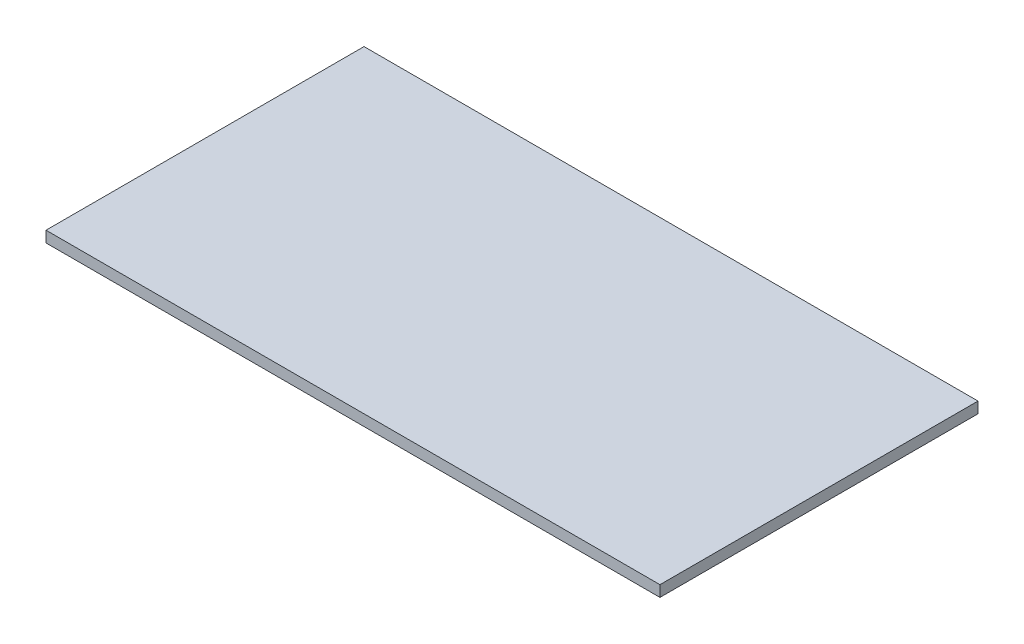
SolidWorks part; units mm, degrees
ref_plane "前视基准面" through (0, 0, 0) normal (0, 0, 1) x (1, 0, 0)
ref_plane "上视基准面" through (0, 0, 0) normal (0, 1, 0) x (1, 0, 0)
ref_plane "右视基准面" through (0, 0, 0) normal (1, 0, 0) x (0, 0, -1)
sketch "草图1" plane through (0, 0, 0) normal (0, 1, 0) x (1, 0, 0)
  line L1 (0, 0) -> (100, 0)
  line L2 (0, 0) -> (0, 51.8)
  line L3 (0, 51.8) -> (100, 51.8)
  line L4 (100, 0) -> (100, 51.8)
  dimension "D1" = 100
  dimension "D2" = 51.8
extrude "凸台-拉伸1" add sketch "草图1" along normal blind 1.8
